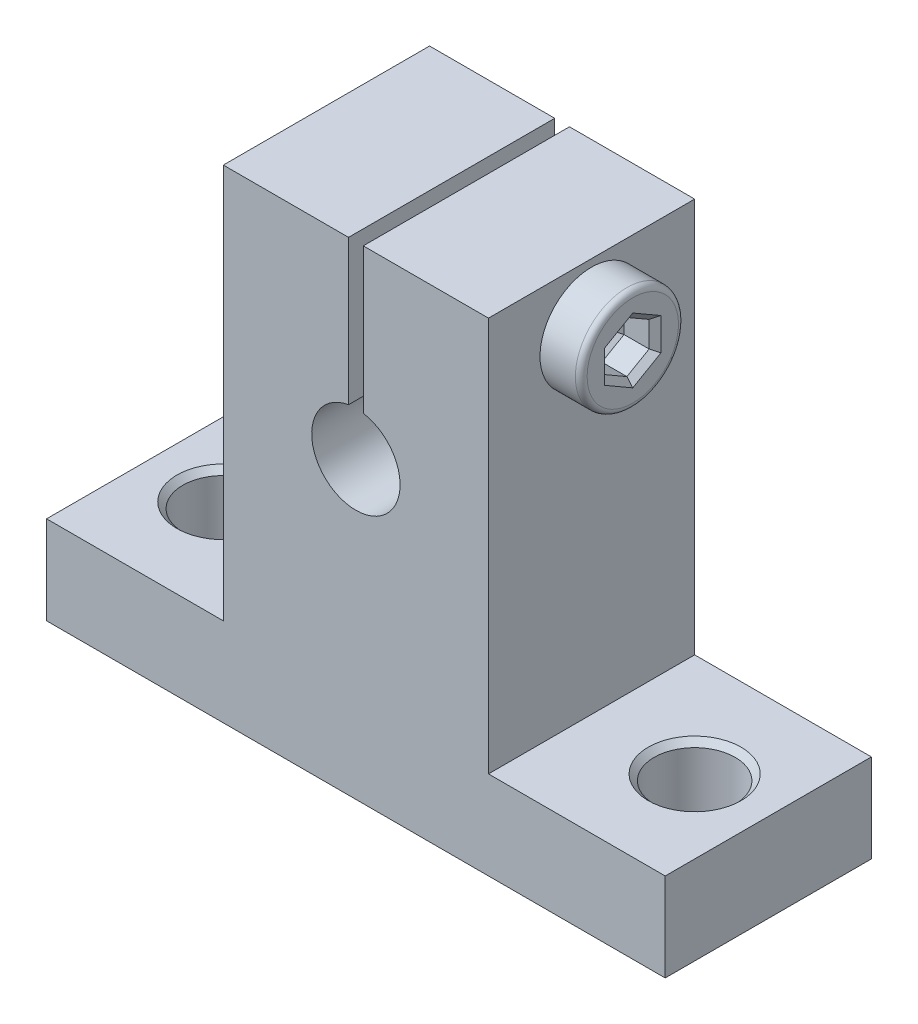
SolidWorks part; units mm, degrees
material "Lega 6061"
ref_plane "Front" through (0, 0, 0) normal (0, 0, 1) x (1, 0, 0)
ref_plane "Top" through (0, 0, 0) normal (0, 1, 0) x (1, 0, 0)
ref_plane "Right" through (0, 0, 0) normal (1, 0, 0) x (0, 0, -1)
sketch "Sketch1" plane through (0, 0, 0) normal (0, 0, 1) x (1, 0, 0)
  line L0 (0, 32.8) -> (0, -11.1975) construction
  line L1 (-21, 0) -> (21, 0)
  line L2 (-21, 0) -> (-21, 6)
  line L3 (-21, 6) -> (-9, 6)
  line L4 (21, 0) -> (21, 6)
  line L5 (9, 6) -> (21, 6)
  line L7 (-9, 6) -> (-9, 32.8)
  line L8 (-9, 32.8) -> (9, 32.8)
  line L9 (9, 6) -> (9, 32.8)
  circle A0 centre (0, 20) radius 3
  dimension "D4" = 6
  dimension "D1" = 6
  dimension "D2" = 42
  dimension "D3" = 18
  dimension "D5" = 32.8
  dimension "20" = 20
extrude "Boss-Extrude1" add sketch "Sketch1" along normal blind 14
sketch "Sketch2" plane through (9, 0, 0) normal (1, 0, 0) x (0, 0, -1)
  line L0 (-14, 32.8) -> (0, 32.8) construction
  line L1 (-7, 32.8) -> (-7, 14.0812) construction
  circle A0 centre (-7, 28.8) radius 2
  dimension "D1" = 4
  dimension "D2" = 4
sketch "Sketch3" plane through (0, 0, 14) normal (0, 0, 1) x (1, 0, 0)
  line L0 (9, 32.8) -> (-9, 32.8) construction
  line L1 (-0.5, 32.8) -> (0.5, 32.8)
  line L2 (-0.5, 32.8) -> (-0.5, 21.0098)
  line L3 (-0.5, 21.0098) -> (0.5, 21.0098)
  line L4 (0.5, 32.8) -> (0.5, 21.0098)
  line L5 (0, 32.8) -> (0, 12.111) construction
  dimension "D1" = 1
extrude "Cut-Extrude1" cut sketch "Sketch3" against normal blind 19 contours L4 L3 L2 L1
extrude "Cut-Extrude3" cut sketch "Sketch2" against normal blind 31 contours A0
sketch "Sketch5" plane through (0, 6, 0) normal (0, 1, 0) x (1, 0, 0)
  line L0 (0, 7.6779) -> (0, -23.3122) construction
  line L1 (21, -7) -> (-21, -7) construction
  line L4 (21, -14) -> (21, 0) construction
  line L5 (-21, -14) -> (-21, 0) construction
  circle A0 centre (16, -7) radius 2.75
  circle A1 centre (-16, -7) radius 2.75
  dimension "D1" = 32
  dimension "D2" = 5.5
extrude "Cut-Extrude5" cut sketch "Sketch5" against normal blind 22
ref_plane "Piano1" through (0, 0, 7) normal (0, 0, 1) x (1, 0, 0)
sketch "Schizzo1" plane through (0, 0, 7) normal (0, 0, 1) x (1, 0, 0)
  line L0 (-22.7047, 28.8) -> (19.8969, 28.8) construction
  line L4 (11.8, 28.8) -> (-11, 28.8)
  line L5 (-11, 28.8) -> (-11, 30.4)
  line L6 (-10.6, 30.8) -> (9, 30.8)
  line L12 (9, 32.8) -> (0.5, 32.8) construction
  line L13 (-11, 30.4) -> (-10.6, 30.8)
  line L14 (9, 30.8) -> (9, 32.3)
  line L15 (9, 32.3) -> (11.8, 32.3)
  line L16 (11.8, 32.3) -> (11.8, 28.8)
  line L17 (9, 6) -> (9, 32.8) construction
  point P7 (-11, 30.8)
  dimension "D1" = 22.8
  dimension "D2" = 3.5
  dimension "D3" = 2.8
  dimension "D6" = 2
  dimension "D7" = 2
revolve "Rivoluzione1" add sketch "Schizzo1" angle 360 about L0
cosmetic thread "Filettatura cosmetica1" parameters "D2"=3.22
sketch "Schizzo2" plane through (11.8, 0, 0) normal (1, 0, 0) x (0, 0, -1)
  line L1 (-7, 30.5383) -> (-8.5054, 29.6691)
  line L2 (-8.5054, 29.6691) -> (-8.5054, 27.9309)
  line L3 (-8.5054, 27.9309) -> (-7, 27.0617)
  line L4 (-7, 27.0617) -> (-5.4946, 27.9309)
  line L5 (-5.4946, 27.9309) -> (-5.4946, 29.6691)
  line L6 (-5.4946, 29.6691) -> (-7, 30.5383)
  circle A0 centre (-7, 28.8) radius 1.5 construction
  circle A1 centre (-7, 28.8) radius 1.5054 construction
  dimension "D1" = 3
  dimension "D2" = 1.5054
extrude "Taglio-Estrusione1" cut sketch "Schizzo2" against normal blind 2.5
chamfer "Smusso1" distance 0.4 angle 45 12 edges at (11.8, 28.8, 8.5054) (11.8, 27.4963, 7.7527) (11.8, 27.4963, 6.2473) (11.8, 28.8, 5.4946) (11.8, 30.1037, 6.2473) (11.8, 30.1037, 7.7527) (9.3, 28.8, 5.4946) (9.3, 27.4963, 6.2473) (9.3, 27.4963, 7.7527) (9.3, 28.8, 8.5054) (9.3, 30.1037, 7.7527) (9.3, 30.1037, 6.2473)
fillet "Raccordo1" radius 0.4 1 edges at (11.8, 25.3, 7)
chamfer "Smusso2" distance 0.4 angle 45 2 edges at (13.25, 6, 7) (-13.25, 6, 7)
